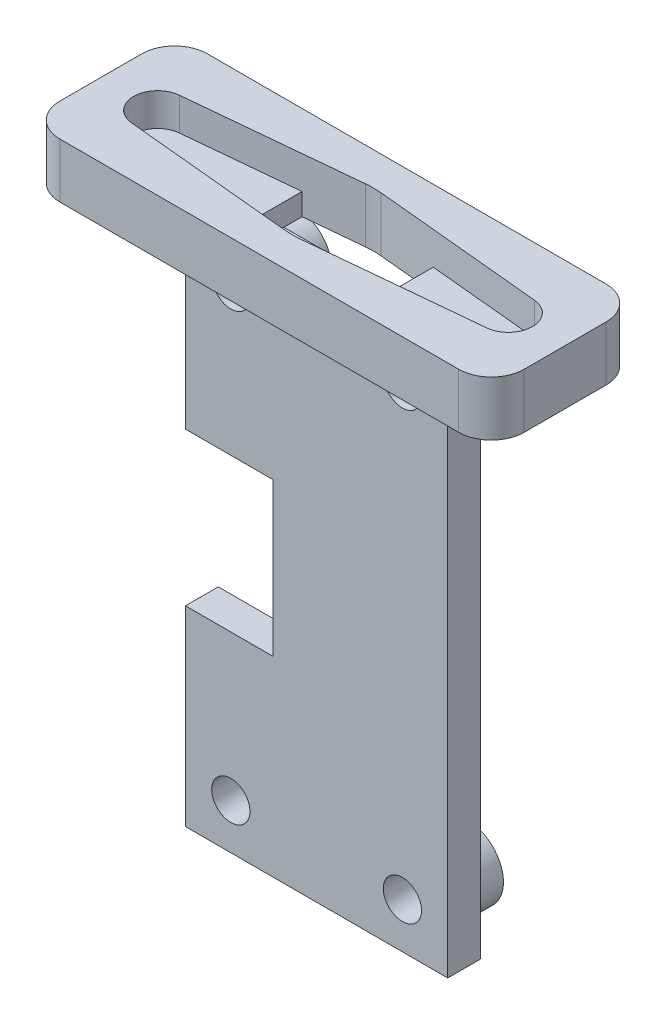
SolidWorks part; units mm, degrees
ref_plane "Front Plane" through (0, 0, 0) normal (0, 0, 1) x (1, 0, 0)
ref_plane "Top Plane" through (0, 0, 0) normal (0, 1, 0) x (1, 0, 0)
ref_plane "Right Plane" through (0, 0, 0) normal (1, 0, 0) x (0, 0, -1)
sketch "Sketch1" plane through (0, 0, 0) normal (0, 1, 0) x (1, 0, 0)
  line L0 (-18.25, 0) -> (18.25, 0) construction
  line L1 (-18.25, -3.75) -> (18.25, -3.75) construction
  line L2 (-18.25, -3.75) -> (-18.25, 3.75) construction
  line L3 (-18.25, 3.75) -> (18.25, 3.75) construction
  line L4 (18.25, -3.75) -> (18.25, 3.75) construction
  line L5 (-18.25, -3.75) -> (18.25, 3.75) construction
  line L6 (-18.25, 3.75) -> (18.25, -3.75) construction
  line L7 (-18.25, 6.75) -> (18.25, 6.75)
  line L8 (-21.25, 3.75) -> (-21.25, -3.75)
  line L9 (-18.25, -6.75) -> (18.25, -6.75)
  line L10 (21.25, 3.75) -> (21.25, -3.75)
  line L11 (-21.25, 6.75) -> (21.25, -6.75) construction
  line L12 (-21.25, -6.75) -> (21.25, 6.75) construction
  line L13 (16.2601, 2.1899) -> (0.7163, 3.6813)
  line L14 (16.2601, -2.1899) -> (0.7163, -3.6813)
  line L15 (0, -3.75) -> (0, 0) construction
  line L16 (-16.2601, -2.1899) -> (-0.7163, -3.6813)
  line L17 (-16.2601, 2.1899) -> (-0.7163, 3.6813)
  arc A0 (-18.25, 6.75) -> (-21.25, 3.75) centre (-18.25, 3.75) ccw
  arc A1 (-21.25, -3.75) -> (-18.25, -6.75) centre (-18.25, -3.75) ccw
  arc A2 (21.25, -3.75) -> (18.25, -6.75) centre (18.25, -3.75) cw
  arc A3 (21.25, 3.75) -> (18.25, 6.75) centre (18.25, 3.75) ccw
  arc A4 (16.2601, -2.1899) -> (16.2601, 2.1899) centre (16.05, 0) ccw
  arc A5 (-16.2601, -2.1899) -> (-16.2601, 2.1899) centre (-16.05, 0) cw
  arc A6 (0.7163, -3.6813) -> (-0.7163, -3.6813) centre (0, 3.7844) cw
  arc A7 (0.7163, 3.6813) -> (-0.7163, 3.6813) centre (0, -3.7844) ccw
  point P0 (0, 0)
  point P6 (0, 0)
  point P39 (0, 3.75)
  dimension "D5" = 3
  dimension "D8" = 7.5
  dimension "D1" = 36.5
  dimension "D2" = 7.5
  dimension "D3" = 3
  dimension "D4" = 3
  dimension "D6" = 2.2
  dimension "D7" = 3.75
extrude "Boss-Extrude1" add sketch "Sketch1" along normal blind 5
sketch "Sketch2" plane through (0, 0, 0) normal (0, -1, 0) x (1, 0, 0)
  line L0 (-16.2601, 2.1899) -> (-6, 3.1743)
  line L1 (-16.2601, -2.1899) -> (-6, -3.1743)
  line L2 (6, -3.1743) -> (16.2601, -2.1899)
  line L3 (16.2601, 2.1899) -> (6, 3.1743)
  line L4 (6, 3.1743) -> (6, -3.1743)
  line L5 (-6, 3.1743) -> (-6, -3.1743)
  line L6 (16.2601, -2.1899) -> (0.7163, -3.6813) construction
  arc A0 (-0.7163, 3.6813) -> (0.7163, 3.6813) centre (0, -3.7844) cw construction
  arc A1 (0.7163, -3.6813) -> (-0.7163, -3.6813) centre (0, 3.7844) cw construction
  arc A2 (-16.2601, 2.1899) -> (-16.2601, -2.1899) centre (-16.05, 0) ccw
  arc A3 (16.2601, -2.1899) -> (16.2601, 2.1899) centre (16.05, 0) ccw
  point P24 (0, 0)
  dimension "D1" = 6
  dimension "D2" = 12
extrude "Boss-Extrude2" add sketch "Sketch2" against normal blind 2
sketch "Sketch4" plane through (0, 0, 0) normal (0, -1, 0) x (1, 0, 0)
  line L1 (12, 1.5) -> (-12, 1.5)
  line L2 (12, 1.5) -> (12, -1.5)
  line L3 (12, -1.5) -> (-12, -1.5)
  line L4 (-12, 1.5) -> (-12, -1.5)
  line L5 (12, 1.5) -> (-12, -1.5) construction
  line L6 (12, -1.5) -> (-12, 1.5) construction
  point P0 (0, 0)
  dimension "D1" = 3
  dimension "D2" = 24
extrude "Boss-Extrude3" add sketch "Sketch4" along normal blind 49
sketch "Sketch5" plane through (0, 0, -1.5) normal (0, 0, -1) x (-1, 0, 0)
  line L0 (-6, 0) -> (-12, 0) construction
  line L1 (12, -49) -> (12, 0) construction
  line L2 (12, 0) -> (6, 0) construction
  line L3 (12, -17.5) -> (4, -17.5)
  line L4 (12, -17.5) -> (12, -31.5)
  line L5 (12, -31.5) -> (4, -31.5)
  line L6 (4, -17.5) -> (4, -31.5)
  circle A2 centre (7.85, -44.85) radius 1.75
  circle A3 centre (-7.85, -44.85) radius 1.75
  circle A4 centre (-7.85, -4.15) radius 1.75
  circle A5 centre (7.85, -4.15) radius 1.75
  dimension "D1" = 15.7
  dimension "D2" = 3.5
  dimension "D3" = 3.5
  dimension "D4" = 3.5
  dimension "D5" = 3.5
  dimension "D6" = 40.7
  dimension "D7" = 4.15
  dimension "D8" = 4.15
  dimension "D9" = 14
  dimension "D10" = 8
  dimension "D11" = 17.5
extrude "Cut-Extrude1" cut sketch "Sketch5" against normal up to next
sketch "Sketch6" plane through (0, 0, -1.5) normal (0, 0, -1) x (-1, 0, 0)
  circle A0 centre (-7.85, -4.15) radius 1.75
  circle A1 centre (7.85, -4.15) radius 1.75
  circle A2 centre (7.85, -44.85) radius 1.75
  circle A3 centre (-7.85, -44.85) radius 1.75
  circle A4 centre (-7.85, -4.15) radius 1.75 construction
  circle A5 centre (-7.85, -4.15) radius 3.25
  circle A6 centre (7.85, -4.15) radius 3.25
  circle A7 centre (7.85, -44.85) radius 3.25
  circle A8 centre (-7.85, -44.85) radius 3.25
  dimension "D1" = 1.5
extrude "Boss-Extrude4" add sketch "Sketch6" along normal blind 3
